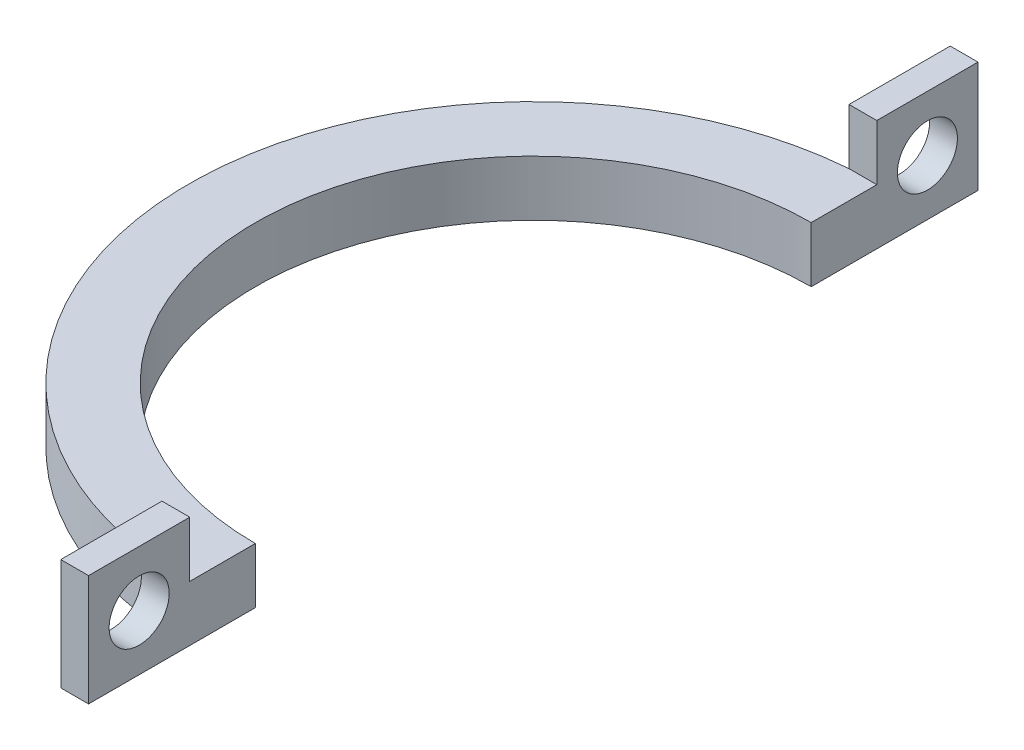
SolidWorks part; units mm, degrees
ref_plane "Front Plane" through (0, 0, 0) normal (0, 0, 1) x (1, 0, 0)
ref_plane "Top Plane" through (0, 0, 0) normal (0, 1, 0) x (1, 0, 0)
ref_plane "Right Plane" through (0, 0, 0) normal (1, 0, 0) x (0, 0, -1)
sketch "Sketch1" plane through (0, 0, 0) normal (0, 1, 0) x (1, 0, 0)
  line L0 (0, -25) -> (0, -40)
  line L1 (0, -55) -> (0, 55) construction
  line L2 (0, -40) -> (-2.5, -40)
  line L3 (-2.5, -40) -> (-2.5, -24.8747)
  line L4 (-55, 0) -> (55, 0) construction
  line L5 (0, 40) -> (-2.5, 40)
  line L6 (0, 25) -> (0, 40)
  line L7 (-2.5, 40) -> (-2.5, 24.8747)
  circle A0 centre (0, 0) radius 25
  circle A1 centre (0, 0) radius 31
  dimension "D1" = 50
  dimension "D2" = 6
  dimension "D3" = 15
  dimension "D4" = 2.5
extrude "Boss-Extrude1" add sketch "Sketch1" along normal blind 5 contours L7 A1 L3 A0 | L3 A1 L0 A0 | A1 L3 L2 L0 | L6 A1 L7 A0 | A1 L6 L5 L7
sketch "Sketch2" plane through (0, 5, 0) normal (0, 1, 0) x (1, 0, 0)
  line L0 (-2.5, 30.899) -> (0, 30.899)
  line L1 (0, -55) -> (0, 55) construction
  line L2 (0, 30.899) -> (0, 40)
  line L3 (0, 40) -> (-2.5, 40) construction
  line L4 (0, 40) -> (-2.5, 40)
  line L5 (-2.5, 40) -> (-2.5, 30.899)
  line L6 (-2.5, -40) -> (0, -40)
  line L7 (0, -40) -> (-2.5, -40) construction
  line L8 (0, -40) -> (0, -30.899)
  line L9 (0, -30.899) -> (-2.5, -30.899)
  line L10 (-2.5, -30.899) -> (-2.5, -40)
extrude "Boss-Extrude2" add sketch "Sketch2" along normal blind 5
sketch "Sketch3" plane through (-2.5, 0, 0) normal (-1, 0, 0) x (0, 0, 1)
  line L1 (-30.899, 0) -> (-40, 0) construction
  line L2 (-30.899, 0) -> (-30.899, 10) construction
  line L3 (-30.899, 10) -> (-40, 10) construction
  line L4 (-40, 0) -> (-40, 10) construction
  line L5 (-30.899, 0) -> (-40, 10) construction
  line L6 (-30.899, 10) -> (-40, 0) construction
  line L7 (-30.899, 10) -> (-30.899, 5) construction
  line L8 (0, -5.5) -> (0, 5.5) construction
  circle A0 centre (-35.4495, 5) radius 2.7
  circle A1 centre (35.4495, 5) radius 2.7
  point P0 (-35.4495, 5)
  dimension "D1" = 5.4
extrude "Cut-Extrude1" cut sketch "Sketch3" against normal up to next
